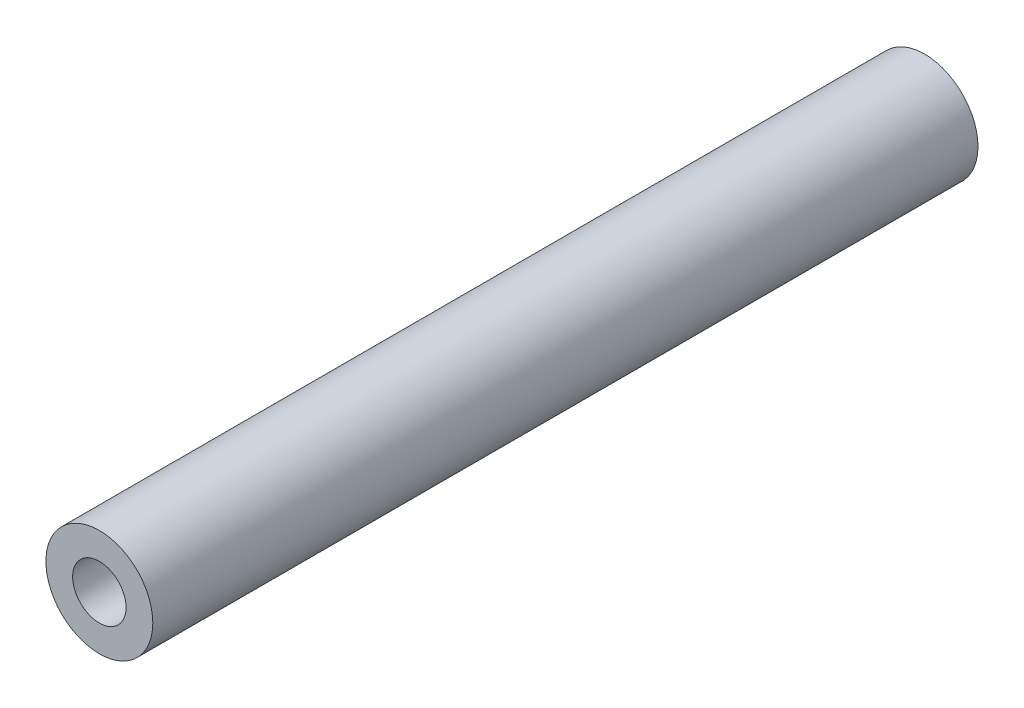
SolidWorks part; units mm, degrees
ref_plane "正面" through (0, 0, 0) normal (0, 0, 1) x (1, 0, 0)
ref_plane "平面" through (0, 0, 0) normal (0, 1, 0) x (1, 0, 0)
ref_plane "右側面" through (0, 0, 0) normal (1, 0, 0) x (0, 0, -1)
sketch "ｽｹｯﾁ6" plane through (0, 0, 0) normal (0, 0, 1) x (1, 0, 0)
  circle A0 centre (0, 0) radius 2.5
  dimension "D1" = 5
extrude "ﾎﾞｽ - 押し出し2" add sketch "ｽｹｯﾁ6" along normal mid plane 38.6
sketch "ｽｹｯﾁ7" plane through (0, 0, -19.3) normal (0, 0, -1) x (-1, 0, 0)
  circle A0 centre (0, 0) radius 1.5076
sketch "ｽｹｯﾁ8" plane through (0, 0, 19.3) normal (0, 0, 1) x (1, 0, 0)
  circle A0 centre (0, 0) radius 1.2838
hole_wizard "M3x0.5 ねじ穴3" positions "3Dｽｹｯﾁ3" profile "ｽｹｯﾁ9" tap size "M3x0.5" standard "JIS"
sketch3d "3Dｽｹｯﾁ3"
  point P0 (0, 0, 19.3)
  point P3 (0, 0, -19.3)
sketch "ｽｹｯﾁ9" plane through (0, 0, 19.3) normal (1, 0, 0) x (0, -1, 0)
  line L0 (0, 0) -> (0, 9.2511)
  line L1 (0, 9.2511) -> (1.25, 8.5)
  line L2 (1.25, 8.5) -> (1.25, 0)
  line L5 (1.25, 0) -> (0, 0)
  line L10 (0, 9.2511) -> (-1.25, 8.5) construction
  line L11 (0, -6.35) -> (0, 107.95) construction
  dimension "ねじ下穴ﾄﾞﾘﾙ直径" = 2.5
  dimension "ねじ下穴ﾄﾞﾘﾙの深さ" = 8.5
  dimension "ﾄﾞﾘﾙ角度" = 118
cosmetic thread "穴のねじ山6"
cosmetic thread "穴のねじ山7"
